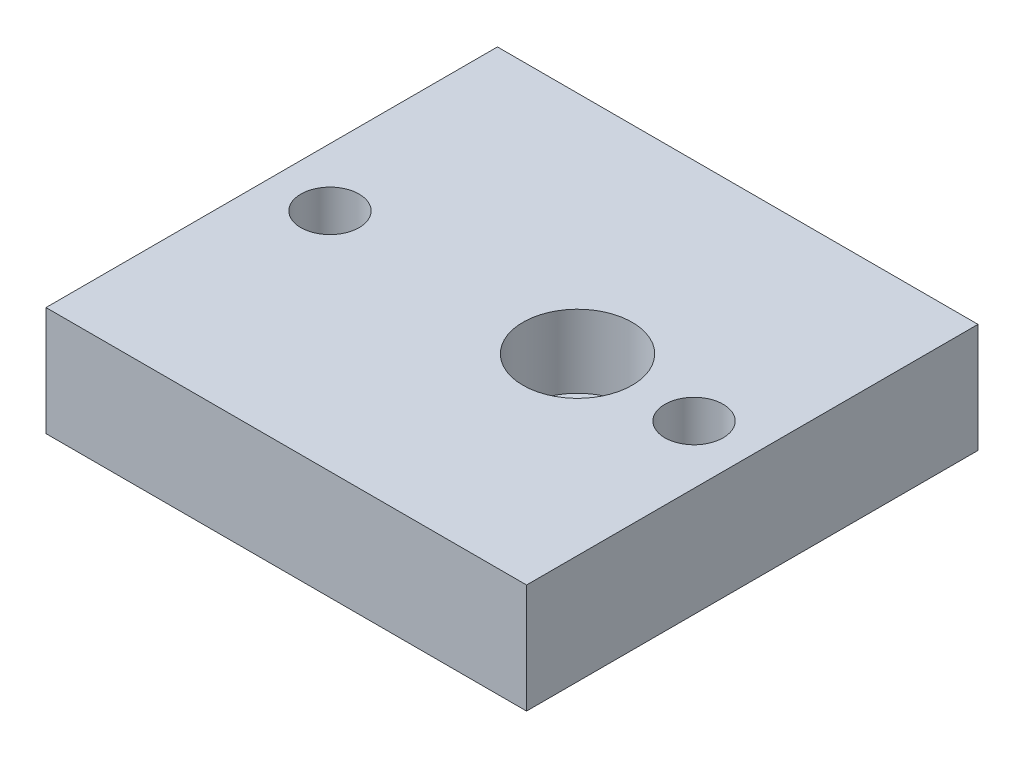
SolidWorks part; units mm, degrees
ref_plane "Alzado" through (0, 0, 0) normal (0, 0, 1) x (1, 0, 0)
ref_plane "Planta" through (0, 0, 0) normal (0, 1, 0) x (1, 0, 0)
ref_plane "Vista lateral" through (0, 0, 0) normal (1, 0, 0) x (0, 0, -1)
sketch "Croquis1" plane through (0, 0, 0) normal (0, 1, 0) x (1, 0, 0)
  line L1 (-33, -31) -> (33, -31)
  line L2 (-33, -31) -> (-33, 31)
  line L3 (-33, 31) -> (33, 31)
  line L4 (33, -31) -> (33, 31)
  line L5 (-33, -31) -> (33, 31) construction
  line L6 (-33, 31) -> (33, -31) construction
  point P0 (0, 0)
  dimension "D1" = 62
  dimension "D2" = 66
extrude "Saliente-Extruir1" add sketch "Croquis1" along normal blind 15
sketch "Croquis2" plane through (0, 15, 0) normal (0, 1, 0) x (1, 0, 0)
  line L0 (-33, 0) -> (33, 0) construction
  line L1 (-33, 31) -> (-33, -31) construction
  line L2 (33, -31) -> (33, 31) construction
  circle A0 centre (9, 0) radius 5
  circle A1 centre (-25, 0) radius 4
  circle A2 centre (25, 0) radius 4
  dimension "D1" = 10
  dimension "D2" = 8
  dimension "D3" = 8
  dimension "D4" = 50
  dimension "D5" = 8
  dimension "D6" = 16
extrude "Cortar-Extruir1" cut sketch "Croquis2" against normal blind 15
sketch "Croquis3" plane through (0, 15, 0) normal (0, 1, 0) x (1, 0, 0)
  circle A0 centre (9, 0) radius 7.5
  dimension "D1" = 15
extrude "Cortar-Extruir2" cut sketch "Croquis3" against normal blind 10
